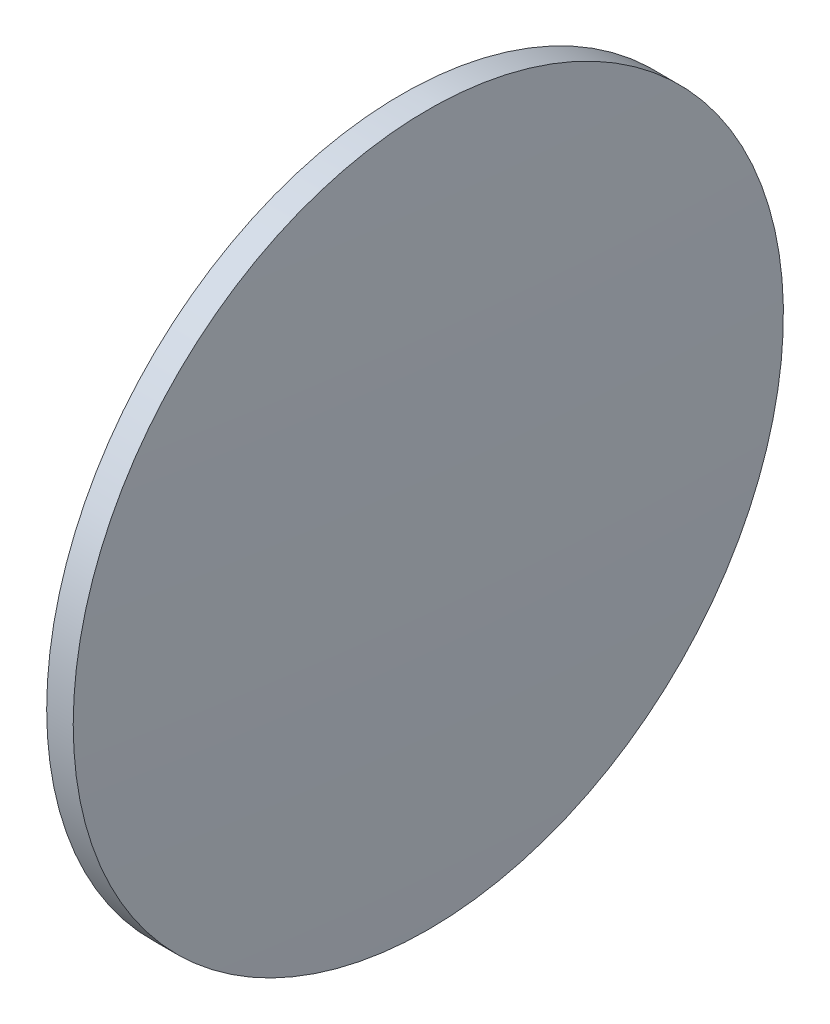
SolidWorks part; units mm, degrees
ref_plane "前视基准面" through (0, 0, 0) normal (0, 0, 1) x (1, 0, 0)
ref_plane "上视基准面" through (0, 0, 0) normal (0, 1, 0) x (1, 0, 0)
ref_plane "右视基准面" through (0, 0, 0) normal (1, 0, 0) x (0, 0, -1)
sketch "草图1" plane through (0, 0, 0) normal (0, 0, 1) x (1, 0, 0)
  line L0 (217.3311, 130.0419) -> (271.1141, 130.0419) construction
  line L1 (236.1561, 130.0419) -> (236.1561, 170.0419)
  line L2 (239.9161, 130.0419) -> (236.1561, 130.0419)
  line L5 (236.1561, 170.0419) -> (239.1461, 170.0419)
  arc A0 (239.9161, 130.0419) -> (239.1461, 170.0419) centre (-799.4299, 130.0419) ccw
revolve "旋转1" add sketch "草图1" angle 360 about L0
